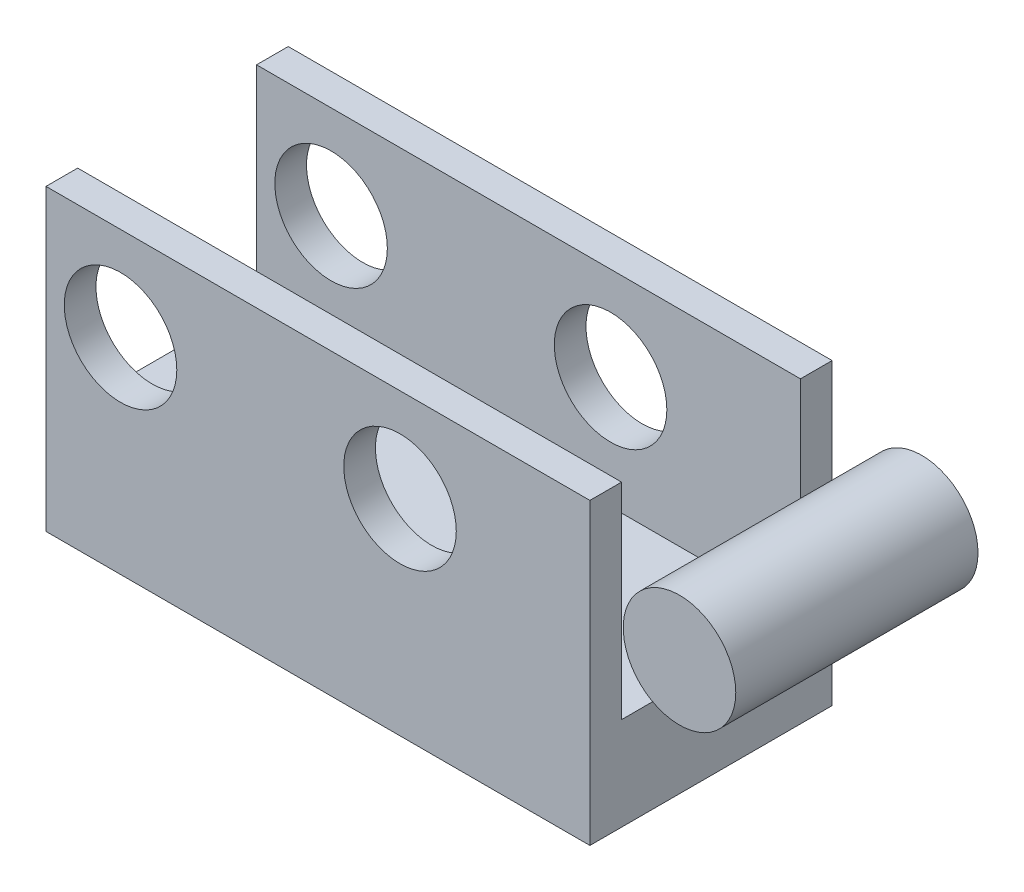
SolidWorks part; units mm, degrees
ref_plane "Front" through (0, 0, 0) normal (0, 0, 1) x (1, 0, 0)
ref_plane "Top" through (0, 0, 0) normal (0, 1, 0) x (1, 0, 0)
ref_plane "Right" through (0, 0, 0) normal (1, 0, 0) x (0, 0, -1)
sketch "Sketch2" plane through (0, 0, 0) normal (0, 0, 1) x (1, 0, 0)
  line L0 (-12.7978, -4.6507) -> (17.2022, -4.6507) construction
  line L6 (-7.2978, 0.3693) -> (7.2978, 0.3693)
  line L7 (17.2022, 0.3693) -> (-12.7978, 0.3693) construction
  line L8 (-7.2978, 0.3693) -> (-7.2978, -7.6507)
  line L9 (-7.2978, -7.6507) -> (7.2978, -7.6507)
  line L10 (7.2978, 0.3693) -> (7.2978, -7.6507)
  circle A1 centre (-5.2978, -2.1407) radius 1.51 construction
  circle A3 centre (9.7022, -2.1407) radius 1.51
  circle A5 centre (-5.2978, -2.1407) radius 1.51
  circle A7 centre (2.2022, -2.1407) radius 1.51
  circle A8 centre (2.2022, -2.1407) radius 1.51 construction
  circle A9 centre (9.7022, -2.1407) radius 1.51 construction
  point P7 (0, 0.3693)
  dimension "D1" = 3
  dimension "D2" = 2
extrude "Boss-Extrude2" add sketch "Sketch2" along normal mid plane 6.5
sketch "Sketch3" plane through (0, 0, 0) normal (0, 0, 1) x (1, 0, 0)
  line L0 (7.2978, -7.6507) -> (7.2978, 0.3693) construction
  line L1 (-7.2978, 0.3693) -> (7.2978, 0.3693)
  line L2 (-7.2978, 0.3693) -> (-7.2978, -5.1507)
  line L4 (7.2978, 0.3693) -> (7.2978, -5.1507)
  line L5 (-12.7978, -4.6507) -> (17.2022, -4.6507) construction
  line L6 (-7.2978, 0.3693) -> (-7.2978, -7.6507) construction
  line L7 (-7.2978, -5.1507) -> (7.2978, -5.1507)
  dimension "D1" = 0.5
extrude "Cut-Extrude4" cut sketch "Sketch3" against normal mid plane 4.8
